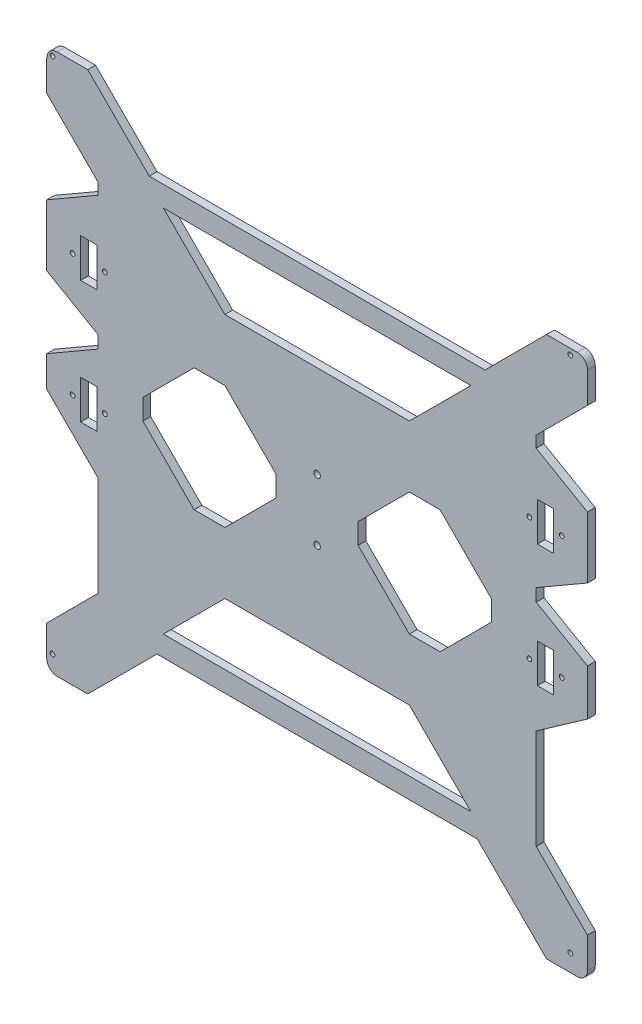
SolidWorks part; units mm, degrees
material "5052-H32"
ref_plane "Front Plane" through (0, 0, 0) normal (0, 0, 1) x (1, 0, 0)
ref_plane "Top Plane" through (0, 0, 0) normal (0, 1, 0) x (1, 0, 0)
ref_plane "Right Plane" through (0, 0, 0) normal (1, 0, 0) x (0, 0, -1)
sketch "Model" plane through (0, 0, 0) normal (0, 0, 1) x (1, 0, 0)
  line L0 (38.5361, 132.6139) -> (38.5361, 132.4727)
  line L1 (38.5361, -178.6774) -> (38.5361, -178.7219)
  line L2 (-253.5639, -197.5861) -> (-253.5639, -197.7273)
  line L3 (-293.0813, -31.2683) -> (-261.3313, -12.9374)
  line L4 (-261.3313, -82.0683) -> (-261.3313, -144.0183)
  line L5 (38.5361, 132.6139) -> (38.5361, 132.4727)
  line L6 (38.5361, -178.6774) -> (38.5361, -178.7219)
  line L7 (10.1687, -144.0183) -> (10.1687, -82.0683)
  line L8 (41.9187, -59.8367) -> (41.9187, -31.2683)
  line L9 (-21.5813, 95.7317) -> (-229.5813, 95.7317)
  line L10 (-293.0813, 108.4317) -> (-261.3313, 76.6817)
  line L11 (-30.3313, -145.5683) -> (-68.4313, -107.4683)
  line L12 (-26.3813, -158.2683) -> (16.5187, -201.1683)
  line L13 (41.9187, 108.4317) -> (41.9187, 127.4817)
  line L14 (-229.5813, 95.7317) -> (-267.6813, 133.8317)
  line L15 (-220.8313, 83.0317) -> (-182.7313, 44.9317)
  line L16 (-277.0813, -45.4288) -> (-257.0813, -45.4288) construction
  line L17 (41.9187, -175.7683) -> (10.1687, -144.0183)
  line L18 (-267.6813, -201.1683) -> (-224.7813, -158.2683)
  line L19 (-182.7313, -107.4683) -> (-68.4313, -107.4683)
  line L20 (-267.0813, -45.4288) -> (-267.0813, -48.3832) construction
  line L21 (10.1687, 76.6817) -> (41.9187, 108.4317)
  line L22 (-21.5813, 95.7317) -> (16.5187, 133.8317)
  line L23 (-30.3313, 83.0317) -> (-68.4313, 44.9317)
  line L24 (41.9187, -31.2683) -> (10.1687, -12.9374)
  line L25 (-261.3313, -144.0183) -> (-293.0813, -175.7683)
  line L26 (-182.7313, 44.9317) -> (-68.4313, 44.9317)
  line L27 (-220.8313, -145.5683) -> (-182.7313, -107.4683)
  line L28 (-220.8313, -145.5683) -> (-30.3313, -145.5683)
  line L29 (-261.3313, -82.0683) -> (-293.0813, -50.3183)
  line L30 (-293.0813, -31.2683) -> (-293.0813, -50.3183)
  line L31 (-277.0813, -43.9683) -> (-277.0813, -31.2683) construction
  line L32 (-261.3313, -12.9374) -> (-261.3313, -5.1492)
  line L33 (-201.7813, -69.3683) -> (-233.5313, -37.6183)
  line L34 (-182.7313, -69.3683) -> (-201.7813, -69.3683)
  line L35 (10.1687, -12.9374) -> (10.1687, -5.1492)
  line L36 (10.1687, -5.1492) -> (41.9187, 13.1817)
  line L37 (-150.9813, -37.6183) -> (-182.7313, -69.3683)
  line L38 (41.9187, -59.8367) -> (12.8646, -80.1806)
  line L39 (12.8646, -80.1806) -> (10.1687, -82.0683)
  line L40 (-100.1813, -37.6183) -> (-100.1813, -24.9183)
  line L41 (-150.9813, -37.6183) -> (-150.9813, -24.9183)
  line L42 (-150.9813, -24.9183) -> (-182.7313, 6.8317)
  line L43 (-182.7313, 6.8317) -> (-201.7813, 6.8317)
  line L44 (-201.7813, 6.8317) -> (-233.5313, -24.9183)
  line L45 (-233.5313, -24.9183) -> (-233.5313, -37.6183)
  line L46 (-17.6313, -24.9183) -> (-17.6313, -37.6183)
  line L47 (-49.3813, 6.8317) -> (-17.6313, -24.9183)
  line L48 (-220.8313, 83.0317) -> (-30.3313, 83.0317)
  line L49 (-68.4313, 6.8317) -> (-49.3813, 6.8317)
  line L50 (-100.1813, -24.9183) -> (-68.4313, 6.8317)
  line L51 (-100.1813, -37.6183) -> (-68.4313, -69.3683)
  line L52 (-68.4313, -69.3683) -> (-49.3813, -69.3683)
  line L53 (-49.3813, -69.3683) -> (-17.6313, -37.6183)
  line L54 (41.9187, 13.1817) -> (41.9187, 51.2817)
  line L55 (41.9187, 51.2817) -> (10.1687, 69.6126)
  line L56 (10.1687, 69.6126) -> (10.1687, 76.6817)
  line L57 (-261.3313, -5.1492) -> (-293.0813, 13.1817)
  line L58 (-267.6813, -201.1683) -> (-286.7313, -201.1683)
  line L59 (-293.0813, -194.8183) -> (-293.0813, -175.7683)
  line L60 (-293.0813, 108.4317) -> (-293.0813, 127.4817)
  line L61 (-286.7313, 133.8317) -> (-267.6813, 133.8317)
  line L62 (16.5187, 133.8317) -> (35.5687, 133.8317)
  line L63 (-293.0813, 13.1817) -> (-293.0813, 51.2817)
  line L64 (41.9187, -175.7683) -> (41.9187, -194.8183)
  line L65 (35.5687, -201.1683) -> (16.5187, -201.1683)
  line L66 (-261.3313, 76.6817) -> (-261.3313, 69.6126)
  line L67 (-261.3313, 69.6126) -> (-293.0813, 51.2817)
  line L68 (-277.0813, 30.5682) -> (-257.0813, 30.5682) construction
  line L69 (-257.0813, 30.5682) -> (25.9187, 30.5682) construction
  line L70 (25.9187, 30.5682) -> (25.9187, -45.4288) construction
  line L71 (-224.7813, -158.2683) -> (-26.3813, -158.2683)
  line L72 (38.5361, -178.6774) -> (38.5361, -178.7219)
  line L73 (5.9187, 30.5682) -> (5.9187, -45.4288) construction
  line L74 (-224.7813, -158.2683) -> (-26.3813, -158.2683)
  line L75 (38.5361, -178.6774) -> (38.5361, -178.7219)
  line L76 (-277.0813, 30.5682) -> (-277.0813, -45.4288) construction
  line L77 (-125.5813, 95.7317) -> (-125.5813, -158.2683) construction
  line L78 (-293.0813, -31.2683) -> (41.9187, -31.2683) construction
  arc A0 (35.5687, -201.1683) -> (41.9187, -194.8183) centre (35.5687, -194.8183) ccw
  arc A1 (-293.0813, -194.8183) -> (-286.7313, -201.1683) centre (-286.7313, -194.8183) ccw
  arc A2 (-293.0813, 127.4817) -> (-286.7313, 133.8317) centre (-286.7313, 127.4817) cw
  arc A3 (35.5687, 133.8317) -> (41.9187, 127.4817) centre (35.5687, 127.4817) cw
  circle A4 centre (-289.5253, -190.6025) radius 1.4605
  circle A5 centre (31.3529, -190.6025) radius 1.4605
  circle A6 centre (31.3529, 130.2757) radius 1.4605
  circle A7 centre (-289.5253, 130.2757) radius 1.4605
  circle A8 centre (-277.0813, -45.4288) radius 1.4605
  circle A9 centre (-257.0813, -45.4288) radius 1.4605
  circle A10 centre (25.9187, -45.4288) radius 1.4605
  circle A11 centre (5.9187, -45.4288) radius 1.4605
  circle A12 centre (25.9187, 30.5682) radius 1.4605
  circle A13 centre (5.9187, 30.5682) radius 1.4605
  circle A14 centre (-257.0813, 30.5682) radius 1.4605
  circle A15 centre (-277.0813, 30.5682) radius 1.4605
  circle A16 centre (-125.5813, -12.2183) radius 2
  circle A17 centre (-125.5813, -50.3183) radius 2
  point P72 (-125.5813, -31.2683)
  point P114 (-125.5813, 83.0317)
  point P120 (-233.5313, -31.2683)
  point P129 (-150.9813, -31.2683)
  point P149 (-125.5813, 44.9317)
  point P156 (-17.6313, -31.2683)
  dimension "D28" = 6.35
  dimension "D29" = 6.35
  dimension "D30" = 6.35
  dimension "D31" = 6.35
  dimension "D35" = 2.921
  dimension "D36" = 2.921
  dimension "D37" = 2.921
  dimension "D38" = 2.921
  dimension "D53" = 2.921
  dimension "D54" = 2.921
  dimension "D56" = 4
  dimension "D57" = 4
  dimension "D62" = 20
  dimension "D1" = 335
  dimension "D2" = 335
  dimension "D3" = 135
  dimension "D4" = 135
  dimension "D5" = 38.1
  dimension "D6" = 135
  dimension "D7" = 120
  dimension "D8" = 19.05
  dimension "D9" = 135
  dimension "D10" = 19.05
  dimension "D11" = 31.75
  dimension "D12" = 190.5
  dimension "D13" = 114.3
  dimension "D14" = 38.1
  dimension "D15" = 114.3
  dimension "D16" = 135
  dimension "D17" = 6.35
  dimension "D18" = 38.1
  dimension "D19" = 135
  dimension "D20" = 135
  dimension "D21" = 6.35
  dimension "D22" = 19.05
  dimension "D23" = 25.4
  dimension "D24" = 50.8
  dimension "D25" = 120
  dimension "D26" = 135
  dimension "D27" = 127
  dimension "D32" = 19.05
  dimension "D33" = 19.05
  dimension "D34" = 19.05
  dimension "D39" = 120
  dimension "D40" = 19.05
  dimension "D41" = 120
  dimension "D42" = 120
  dimension "D43" = 50.8
  dimension "D44" = 19.05
  dimension "D45" = 31.75
  dimension "D46" = 125
  dimension "D47" = 320.8782
  dimension "D48" = 320.8782
  dimension "D49" = 3.556
  dimension "D50" = 3.556
  dimension "D51" = 20
  dimension "D52" = 26
  dimension "D55" = 12.7
  dimension "D58" = 38.1
  dimension "D59" = 19.05
  dimension "D60" = 82.55
  dimension "D61" = 38.1
  dimension "D63" = 120
  dimension "D64" = 38.1
  dimension "D65" = 82.55
  dimension "D67" = 75.997
extrude "Boss-Extrude1" add sketch "Model" along normal mid plane 4.826
sketch "Sketch1" plane through (0, 0, 2.413) normal (0, 0, 1) x (1, 0, 0)
  line L0 (25.9187, 30.5682) -> (25.9187, 17.7506) construction
  line L1 (-272.0813, -33.4288) -> (-262.0813, -33.4288)
  line L2 (-272.0813, -33.4288) -> (-272.0813, -57.4288)
  line L3 (-272.0813, -57.4288) -> (-262.0813, -57.4288)
  line L4 (-262.0813, -33.4288) -> (-262.0813, -57.4288)
  line L5 (-272.0813, 42.5712) -> (-262.0813, 42.5712)
  line L6 (-272.0813, 42.5712) -> (-272.0813, 18.5712)
  line L7 (-272.0813, 18.5712) -> (-262.0813, 18.5712)
  line L8 (-262.0813, 42.5712) -> (-262.0813, 18.5712)
  line L9 (10.9187, 42.5712) -> (20.9187, 42.5712)
  line L10 (10.9187, 42.5712) -> (10.9187, 18.5712)
  line L11 (10.9187, 18.5712) -> (20.9187, 18.5712)
  line L12 (20.9187, 42.5712) -> (20.9187, 18.5712)
  line L13 (10.9187, -33.4288) -> (20.9187, -33.4288)
  line L14 (10.9187, -33.4288) -> (10.9187, -57.4288)
  line L15 (10.9187, -57.4288) -> (20.9187, -57.4288)
  line L16 (20.9187, -33.4288) -> (20.9187, -57.4288)
  circle A1 centre (-277.0813, -45.4288) radius 1.4605 construction
  circle A5 centre (-277.0813, 30.5682) radius 1.4605 construction
  circle A8 centre (25.9187, 30.5682) radius 1.4605 construction
  circle A9 centre (25.9187, -45.4288) radius 1.4605 construction
  point P20 (15.9187, 42.5712)
  dimension "D3" = 12
  dimension "D4" = 5
  dimension "D5" = 10
  dimension "D8" = 100
  dimension "D11" = 100
  dimension "D15" = 12
  dimension "D1" = 10
  dimension "D2" = 24
  dimension "D6" = 24
  dimension "D7" = 5
  dimension "D9" = 24
  dimension "D10" = 5
  dimension "D12" = 10
  dimension "D13" = 10
  dimension "D14" = 24
  dimension "D16" = 5
extrude "Cut-Extrude1" cut sketch "Sketch1" against normal blind 10
